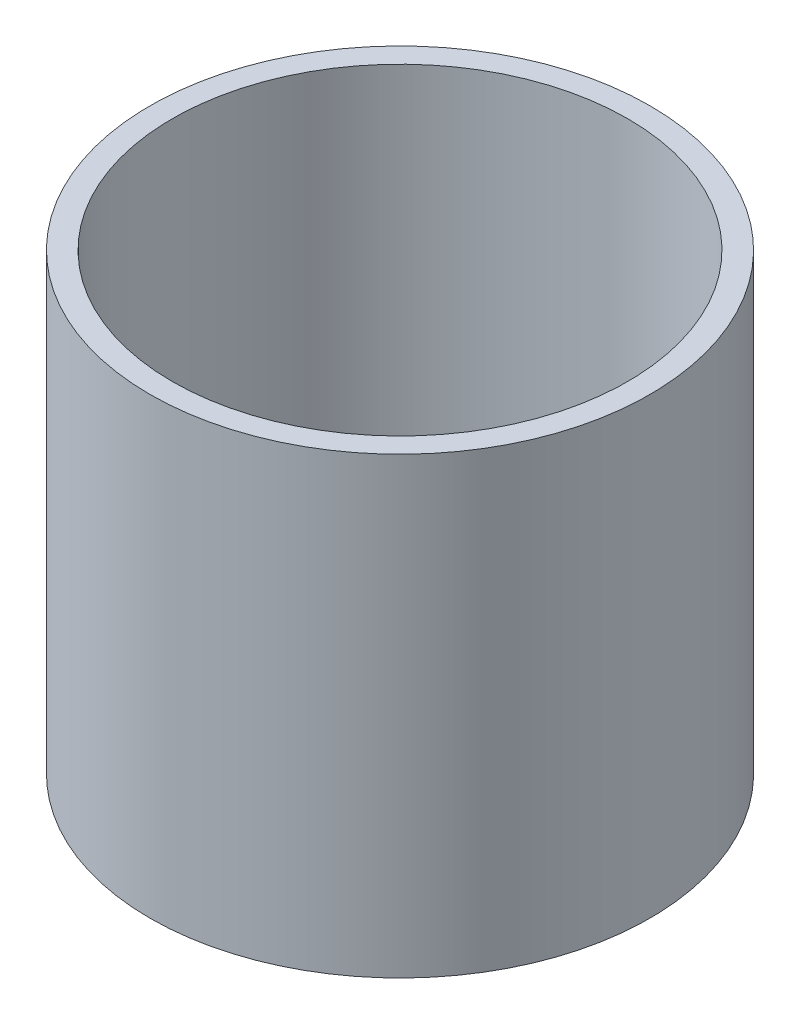
SolidWorks part; units mm, degrees
ref_plane "前视基准面" through (0, 0, 0) normal (0, 0, 1) x (1, 0, 0)
ref_plane "上视基准面" through (0, 0, 0) normal (0, 1, 0) x (1, 0, 0)
ref_plane "右视基准面" through (0, 0, 0) normal (1, 0, 0) x (0, 0, -1)
sketch "草图1" plane through (0, 0, 0) normal (0, 0, 1) x (1, 0, 0)
  line L0 (0, 161.3762) -> (0, 0) construction
  line L1 (141.7365, 0) -> (-131.7984, 0) construction
  line L2 (28, 0) -> (28, 50.8)
  line L3 (25.5, 50.8) -> (28, 50.8)
  line L4 (25.5, 0) -> (28, 0)
  line L7 (25.5, 50.8) -> (25.5, 0)
  dimension "D2" = 28
  dimension "D3" = 50.8
  dimension "D11" = 25.5
revolve "旋转1" add sketch "草图1" angle 360 about L0
cosmetic thread "装饰螺纹线1" parameters "D2"=52
